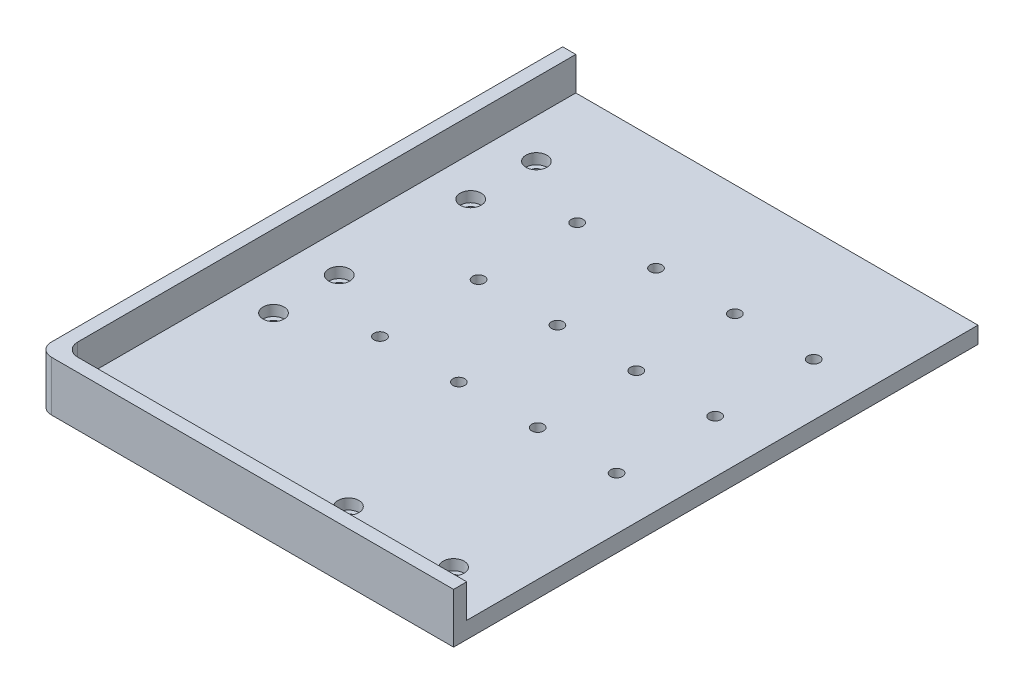
SolidWorks part; units mm, degrees
ref_plane "Front Plane" through (0, 0, 0) normal (0, 0, 1) x (1, 0, 0)
ref_plane "Top Plane" through (0, 0, 0) normal (0, 1, 0) x (1, 0, 0)
ref_plane "Right Plane" through (0, 0, 0) normal (1, 0, 0) x (0, 0, -1)
sketch "Sketch1" plane through (0, 0, 0) normal (0, 1, 0) x (1, 0, 0)
  line L1 (0, 0) -> (158, 0)
  line L2 (0, 0) -> (0, -199.5)
  line L3 (0, -199.5) -> (158, -199.5)
  line L4 (158, 0) -> (158, -199.5)
  dimension "D1" = 158
  dimension "D2" = 199.5
extrude "Boss-Extrude1" add sketch "Sketch1" along normal blind 6.35
sketch "Sketch2" [suppressed] plane through (0, 6.35, 0) normal (0, 1, 0) x (1, 0, 0)
  line L0 (0, -199.5) -> (158, -199.5) construction
  line L1 (81, -199.5) -> (0, -199.5)
  line L2 (81, -199.5) -> (81, -158.5)
  line L3 (81, -158.5) -> (0, -158.5)
  line L4 (0, -199.5) -> (0, -158.5)
  dimension "D1" = 81
  dimension "D2" = 41
sketch "Sketch3" plane through (0, 6.35, 0) normal (0, 1, 0) x (1, 0, 0)
  line L22 (0, 0) -> (0, -199.5) construction
  line L30 (0, -199.5) -> (158, -199.5) construction
  line L34 (0, 0) -> (0, -199.5)
  line L35 (0, -199.5) -> (158, -199.5)
  line L36 (5, 0) -> (5, -194.5)
  line L37 (5, -194.5) -> (158, -194.5)
  line L38 (158, -199.5) -> (158, -194.5)
  line L39 (0, 0) -> (5, 0)
  dimension "D1" = 5
extrude "Boss-Extrude2" add sketch "Sketch3" along normal blind 12.7
sketch "Sketch4" plane through (0, 6.35, 0) normal (0, -1, 0) x (1, 0, 0)
  line L0 (78, 179.5) -> (158, 179.5) construction
  line L3 (0, 199.5) -> (158, 199.5) construction
  line L4 (118, 179.5) -> (118, 188.5903) construction
  line L5 (20, 160) -> (20, 0) construction
  line L7 (158, 0) -> (0, 0) construction
  line L9 (20, 80) -> (152.6176, 80) construction
  line L10 (158, 199.5) -> (158, 0) construction
  line L12 (0, 0) -> (0, 199.5) construction
  point P8 (98, 179.5)
  point P11 (138, 179.5)
  point P20 (20, 130)
  point P21 (20, 105)
  point P22 (20, 30)
  point P23 (20, 80)
  point P24 (20, 55)
  dimension "D1" = 20
  dimension "D2" = 40
  dimension "D3" = 20
  dimension "D4" = 25
  dimension "D5" = 25
  dimension "D6" = 160
  dimension "D7" = 80
hole_wizard "CBORE for M4 SHCS1" positions "Sketch4" profile "Sketch5" counterbore size "M4" standard "ANSI Metric" end condition up to next
sketch "Sketch5" plane through (20, 6.35, 55) normal (1, 0, 0) x (0, 0, 1)
  line L0 (0, 0) -> (0, 6.35)
  line L1 (0, 6.35) -> (2.25, 6.35)
  line L3 (2.25, 6.35) -> (2.25, 4)
  line L4 (2.25, 4) -> (4, 4)
  line L5 (4, 4) -> (4, 0)
  line L7 (4, 0) -> (0, 0)
  line L11 (0, -6.35) -> (0, 107.95) construction
  dimension "Thru Hole Dia." = 4.5
  dimension "Thru Hole Depth" = 6.35
  dimension "C'Bore Dia." = 8
  dimension "C'Bore Depth" = 4
sketch "Sketch7" [suppressed] plane through (0, 0, 0) normal (0, 0, -1) x (-1, 0, 0)
  line L0 (-79, 19.05) -> (-79, 4.7647) construction
  line L2 (-158, 19.05) -> (0, 19.05) construction
  line L3 (-158, 19.05) -> (-29, 19.05)
  line L4 (-158, 19.05) -> (-158, 9.05)
  line L5 (-158, 9.05) -> (-29, 9.05)
  line L6 (-29, 19.05) -> (-29, 9.05)
  line L7 (0, 19.05) -> (0, 0) construction
  line L8 (-158, 6.35) -> (-158, 0) construction
  dimension "D1" = 29
  dimension "D2" = 10
extrude "Cut-Extrude2" [suppressed] cut sketch "Sketch7" against normal up to next
fillet "Fillet1" [suppressed] radius 5
sketch "Sketch8" plane through (0, 6.35, 0) normal (0, 1, 0) x (1, 0, 0)
  line L0 (158, -117.5) -> (50.5497, -117.5) construction
  line L1 (158, -194.5) -> (158, 0) construction
  line L3 (20, -130) -> (20, -105) construction
  point P4 (138, -117.5)
  point P15 (20, -117.5)
  dimension "D1" = 20
hole_wizard "M4 Clearance Hole2" positions "Sketch8" profile "Sketch9" hole size "M4" standard "ANSI Metric" end condition up to next
sketch "Sketch9" plane through (138, 6.35, 117.5) normal (1, 0, 0) x (0, 0, 1)
  line L0 (0, 0) -> (0, 6.35)
  line L1 (0, 6.35) -> (2.25, 6.35)
  line L2 (2.25, 6.35) -> (2.25, 0)
  line L5 (2.25, 0) -> (0, 0)
  line L11 (0, -6.35) -> (0, 107.95) construction
  dimension "Thru Hole Dia." = 4.5
  dimension "Thru Hole Depth" = 6.35
pattern_linear "LPattern1" count 4 spacing 30 along (-1, 0, 0) count 3 spacing 37.5 along (0, 0, -1) of "M4 Clearance Hole2"
fillet "Fillet2" radius 5 2 edges at (5, 12.7, 194.5) (0, 9.525, 199.5)
